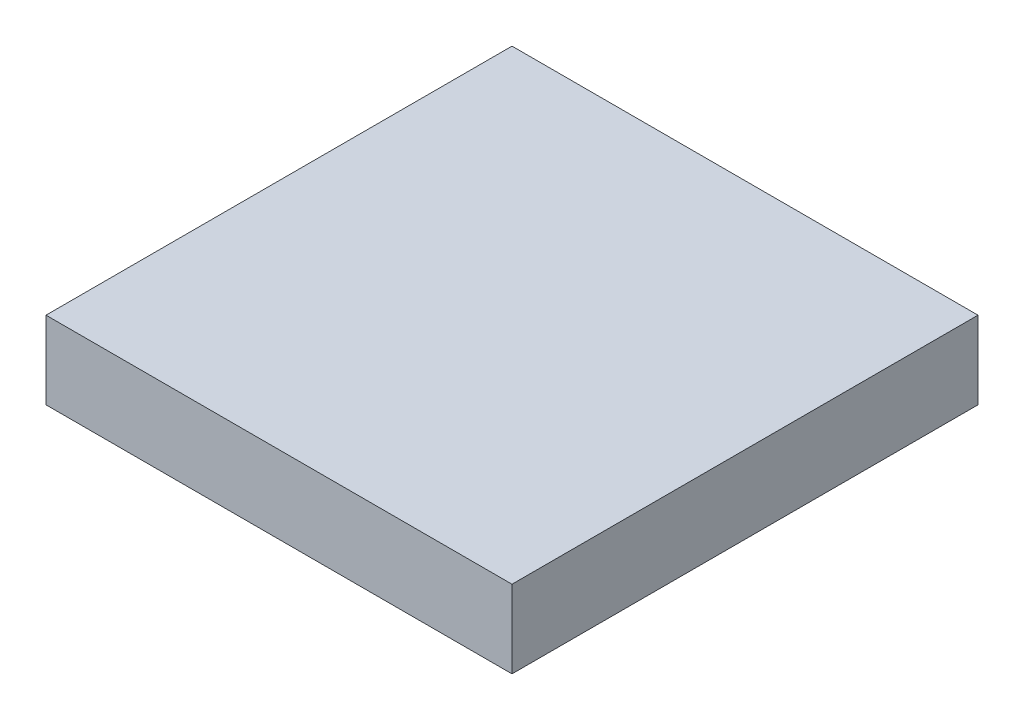
SolidWorks part; units mm, degrees
ref_plane "Front Plane" through (0, 0, 0) normal (0, 0, 1) x (1, 0, 0)
ref_plane "Top Plane" through (0, 0, 0) normal (0, 1, 0) x (1, 0, 0)
ref_plane "Right Plane" through (0, 0, 0) normal (1, 0, 0) x (0, 0, -1)
sketch "Sketch1" plane through (0, 0, 0) normal (0, 1, 0) x (1, 0, 0)
  line L1 (-30, 30) -> (30, 30)
  line L2 (-30, 30) -> (-30, -30)
  line L3 (-30, -30) -> (30, -30)
  line L4 (30, 30) -> (30, -30)
  line L5 (-30, 30) -> (30, -30) construction
  line L6 (-30, -30) -> (30, 30) construction
  point P0 (0, 0)
  dimension "D1" = 60
  dimension "D2" = 60
extrude "Boss-Extrude1" add sketch "Sketch1" along normal blind 10
